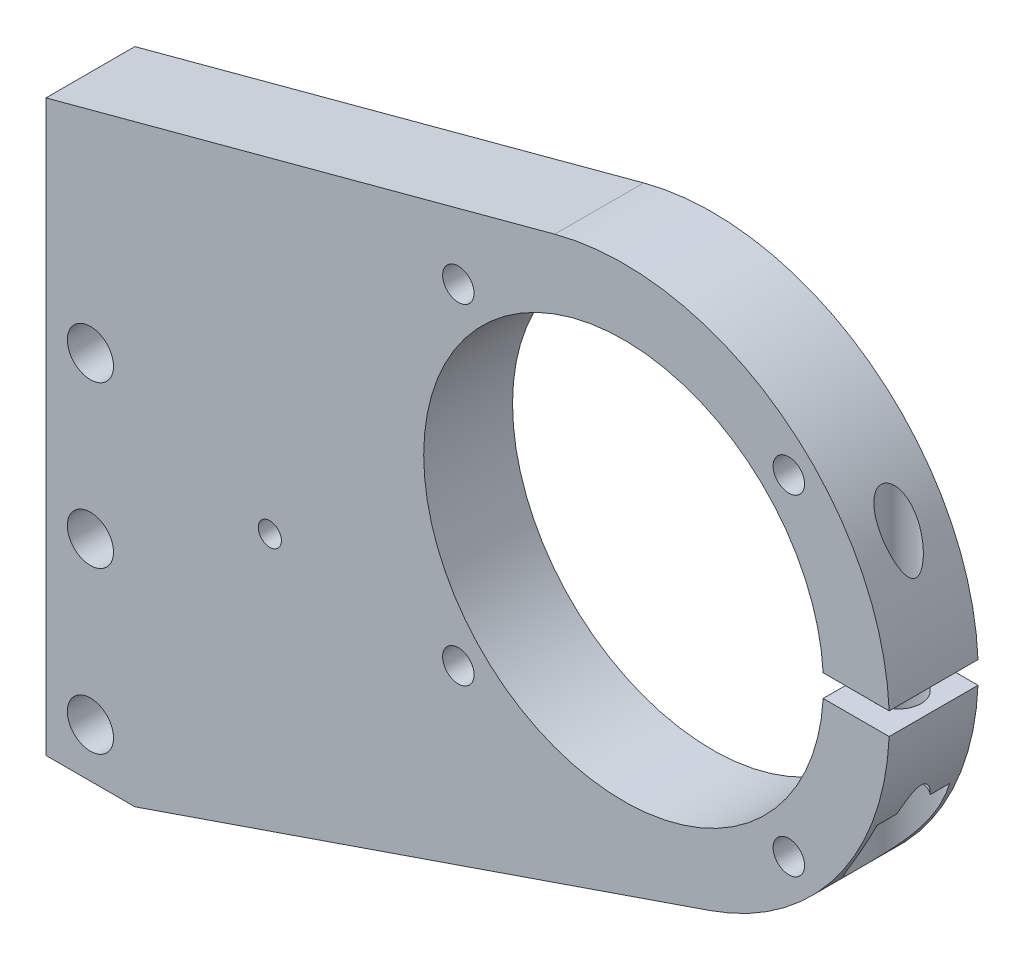
SolidWorks part; units mm, degrees
ref_plane "Front Plane" through (0, 0, 0) normal (0, 0, 1) x (1, 0, 0)
ref_plane "Top Plane" through (0, 0, 0) normal (0, 1, 0) x (1, 0, 0)
ref_plane "Right Plane" through (0, 0, 0) normal (1, 0, 0) x (0, 0, -1)
ref_plane "Plane1" through (0, 0, 0) normal (0, 0, -1) x (-1, 0, 0)
sketch "Sketch1" plane through (0, 0, 0) normal (0, 0, -1) x (-1, 0, 0)
  line L0 (224.1695, 127.7225) -> (151.4352, 147.2116)
  line L1 (129.2465, 74.5705) -> (211.4695, 46.305)
  line L2 (211.4695, 46.305) -> (224.1695, 46.305)
  line L3 (224.1695, 46.305) -> (224.1695, 127.7225)
  arc A0 (151.4352, 147.2116) -> (129.2465, 74.5705) centre (141.6001, 110.5064) ccw
extrude "Boss-Extrude1" add sketch "Sketch1" against normal blind 12.7
sketch "Sketch2" plane through (0, 0, 12.7) normal (0, 0, 1) x (1, 0, 0)
  line L0 (-103.6333, 112.0939) -> (-113.179, 112.0939)
  line L1 (-113.179, 108.9189) -> (-103.6333, 108.9189)
  arc A0 (-103.6333, 108.9189) -> (-103.6333, 112.0939) centre (-141.6001, 110.5064) ccw
  arc A1 (-113.179, 112.0939) -> (-113.179, 108.9189) centre (-141.6001, 110.5064) cw
extrude "Cut-Extrude1" cut sketch "Sketch2" against normal through all
ref_plane "Plane2" through (0, 110.5064, 0) normal (0, 1, 0) x (1, 0, 0)
sketch "Sketch3" plane through (0, 110.5064, 0) normal (0, 1, 0) x (1, 0, 0)
  line L0 (-113.0251, 0) -> (-141.6001, 0)
  line L1 (-141.6001, 0) -> (-141.6001, -12.7)
  line L2 (-141.6001, -12.7) -> (-113.0251, -12.7)
  line L3 (-113.0251, -12.7) -> (-113.0251, 0)
  line L4 (-141.6001, 0) -> (-141.6001, -12.7) construction
  dimension "D1" = 28.575
revolve "Cut-Revolve1" cut sketch "Sketch3" angle 360 about L4
hole_wizard "#8 Clearance Hole1" positions "Sketch5" profile "Sketch4" hole size "#8" standard "ANSI Inch"
sketch "Sketch5" plane through (0, 0, 12.7) normal (0, 0, 1) x (1, 0, 0)
  line L0 (-141.6001, 139.0814) -> (-141.6001, 81.9314) construction
  arc A0 (-113.0692, 112.0939) -> (-113.0692, 108.9189) centre (-141.6001, 110.5064) ccw construction
  point P0 (-117.9781, 86.8844)
  point P1 (-165.2221, 86.8844)
  point P2 (-165.2221, 134.1284)
  point P3 (-117.9781, 134.1284)
  point P12 (-141.6001, 110.5064)
  dimension "D1" = 47.244
  dimension "D2" = 47.244
  dimension "D3" = 23.622
  dimension "D4" = 47.244
  dimension "D5" = 23.622
  dimension "D6" = 23.622
  dimension "D7" = 47.244
  dimension "D8" = 23.622
sketch "Sketch4" plane through (-117.9781, 86.8844, 12.7) normal (1, 0, 0) x (0, -1, 0)
  line L0 (0, 0) -> (0, 12.7)
  line L1 (0, 12.7) -> (2.25, 12.7)
  line L2 (2.25, 12.7) -> (2.25, 0)
  line L5 (2.25, 0) -> (0, 0)
  line L11 (0, -6.35) -> (0, 107.95) construction
  dimension "Thru Hole Dia." = 4.5
  dimension "Thru Hole Depth" = 12.7
hole_wizard "1/4 Clearance Hole1" positions "Sketch7" profile "Sketch6" hole size "1/4" standard "ANSI Inch"
sketch "Sketch7" plane through (0, 0, 0) normal (0, 0, -1) x (-1, 0, 0)
  point P0 (217.8195, 53.305)
  point P1 (217.8195, 76.305)
  point P2 (217.8195, 99.305)
sketch "Sketch6" plane through (-217.8195, 53.305, 0) normal (1, 0, 0) x (0, 1, 0)
  line L0 (0, 0) -> (0, 12.7)
  line L1 (0, 12.7) -> (3.3, 12.7)
  line L2 (3.3, 12.7) -> (3.3, 0)
  line L5 (3.3, 0) -> (0, 0)
  line L11 (0, -6.35) -> (0, 107.95) construction
  dimension "Thru Hole Dia." = 6.6
  dimension "Thru Hole Depth" = 12.7
hole_wizard "#12 Clearance Hole1" positions "Sketch9" profile "Sketch8" hole size "#12" standard "ANSI Inch"
sketch "Sketch9" plane through (0, 0, 12.7) normal (0, 0, 1) x (1, 0, 0)
  point P0 (-192.1695, 89.7225)
sketch "Sketch8" plane through (-192.1695, 89.7225, 12.7) normal (1, 0, 0) x (0, -1, 0)
  line L0 (0, 0) -> (0, 12.7)
  line L1 (0, 12.7) -> (3, 12.7)
  line L2 (3, 12.7) -> (3, 0)
  line L5 (3, 0) -> (0, 0)
  line L11 (0, -6.35) -> (0, 107.95) construction
  dimension "Thru Hole Dia." = 6
  dimension "Thru Hole Depth" = 12.7
ref_plane "Plane3" through (0, 84.1425, 0) normal (0, -1, 0) x (-1, 0, 0)
hole_wizard "Hole1" positions "Sketch11" profile "Sketch10" legacy
sketch "Sketch11" plane through (0, 84.1425, 0) normal (0, -1, 0) x (-1, 0, 0)
  point P0 (108.6333, -6.35)
sketch "Sketch10" plane through (-108.6333, 84.1425, 6.35) normal (1, 0, 0) x (0, 0, -1)
  line L0 (0, 0) -> (0, 24.7764)
  line L1 (0, 24.7764) -> (3.2, 24.7764)
  line L2 (3.2, 24.7764) -> (3.2, 11.7764)
  line L3 (3.2, 11.7764) -> (5.6, 11.7764)
  line L4 (5.6, 11.7764) -> (5.6, 0)
  line L5 (5.6, 0) -> (0, 0)
  line L6 (0, 110) -> (0, -10) construction
  dimension "Diameter" = 6.4
  dimension "Depth" = 24.7764
  dimension "C-Bore Diameter" = 11.2
  dimension "C-Bore Depth" = 11.7764
hole_wizard "#10 Clearance Hole1" positions "Sketch13" profile "Sketch12" hole size "#10" standard "ANSI Inch"
sketch "Sketch13" plane through (0, 112.0939, 0) normal (0, -1, 0) x (-1, 0, 0)
  point P0 (108.6333, -6.35)
sketch "Sketch12" plane through (-108.6333, 112.0939, 6.35) normal (1, 0, 0) x (0, 0, -1)
  line L0 (0, 0) -> (0, 36.4125)
  line L1 (0, 36.4125) -> (2.5, 36.4125)
  line L2 (2.5, 36.4125) -> (2.5, 0)
  line L5 (2.5, 0) -> (0, 0)
  line L11 (0, -6.35) -> (0, 107.95) construction
  dimension "Thru Hole Dia." = 5
  dimension "Thru Hole Depth" = 36.4125
chamfer "Chamfer1" distance 3 angle 45 3 edges at (-221.1195, 53.305, 0) (-221.1195, 76.305, 0) (-221.1195, 99.305, 0)
sketch "Sketch14" plane through (0, 0, 0) normal (0, 0, -1) x (-1, 0, 0)
  circle A0 centre (192.1695, 89.7225) radius 1.651
  circle A1 centre (192.1695, 89.7225) radius 3 construction
  circle A2 centre (192.1695, 89.7225) radius 3
  point P0 (192.1695, 89.7225)
  dimension "D1" = 3.302
extrude "Boss-Extrude2" add sketch "Sketch14" against normal up to surface (12.7 mm away) up to face at (-189.1695, 89.7225, 12.7)
